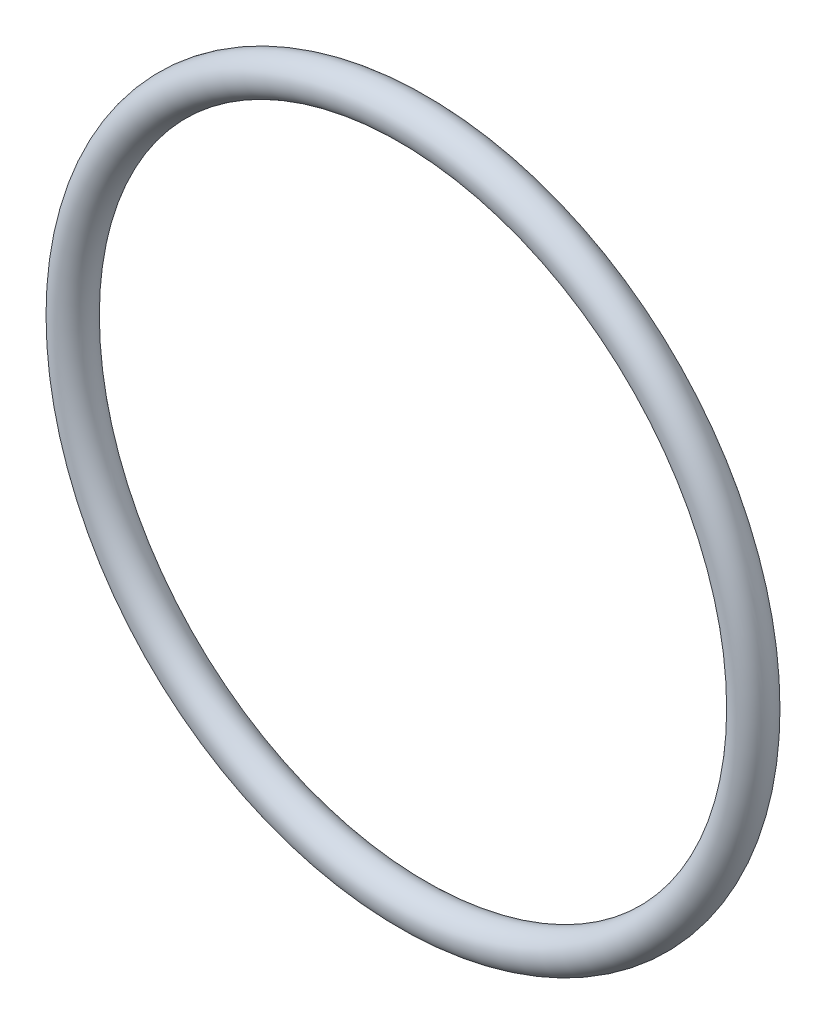
SolidWorks part; units mm, degrees
ref_plane "前视基准面" through (0, 0, 0) normal (0, 0, 1) x (1, 0, 0)
ref_plane "上视基准面" through (0, 0, 0) normal (0, 1, 0) x (1, 0, 0)
ref_plane "右视基准面" through (0, 0, 0) normal (1, 0, 0) x (0, 0, -1)
ref_axis "基准轴1" through (-4.1455, 10.1153, 27.1848) along (0, 0, -1)
sketch "草图1" plane through (1.6048, 9.1014, 0) normal (-0.1736, -0.9848, 0) x (0.9848, -0.1736, 0)
  circle A0 centre (39.2544, 30.8937) radius 2.5
  dimension "D1" = 5
revolve "旋转1" add sketch "草图1" angle 360 about axis through (-4.1455, 10.1153, 27.1848) along (0, 0, -1)
